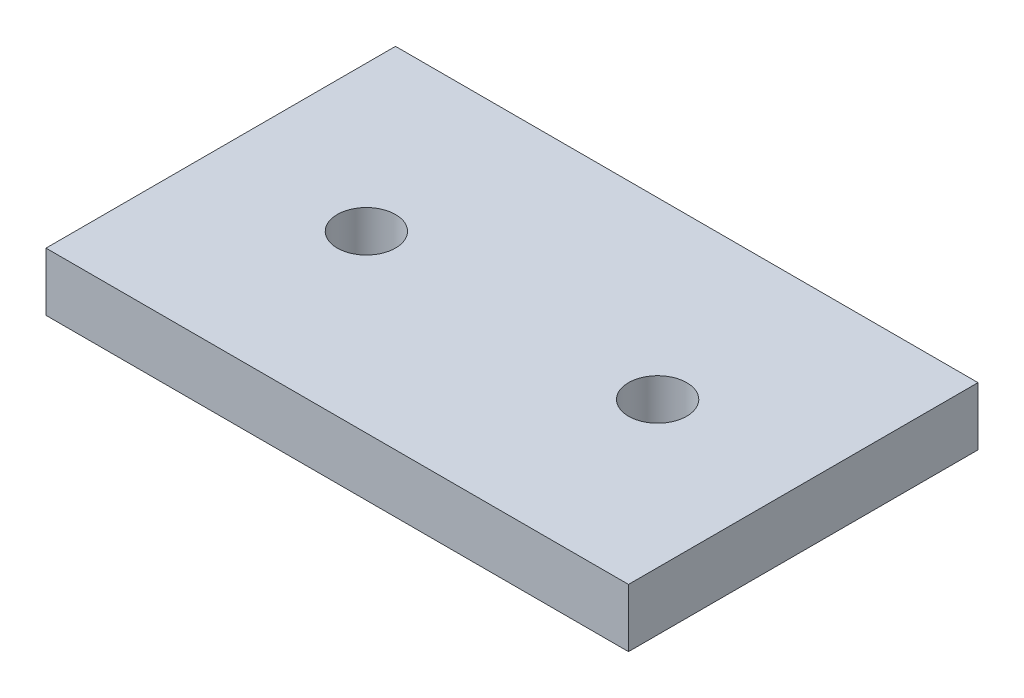
SolidWorks part; units mm, degrees
ref_plane "Спереди" through (0, 0, 0) normal (0, 0, 1) x (1, 0, 0)
ref_plane "Сверху" through (0, 0, 0) normal (0, 1, 0) x (1, 0, 0)
ref_plane "Справа" through (0, 0, 0) normal (1, 0, 0) x (0, 0, -1)
sketch "Эскиз1" plane through (0, 0, 0) normal (0, 1, 0) x (1, 0, 0)
  line L1 (0, 0) -> (100, 0)
  line L2 (0, 0) -> (0, 60)
  line L3 (0, 60) -> (100, 60)
  line L4 (100, 0) -> (100, 60)
extrude "Бобышка-Вытянуть1" add sketch "Эскиз1" along normal blind 10
sketch "Эскиз2" plane through (0, 10, 0) normal (0, 1, 0) x (1, 0, 0)
  circle A0 centre (25, 30) radius 5
  circle A1 centre (75, 30) radius 5
  dimension "D1" = 2
extrude "Вырез-Вытянуть1" cut sketch "Эскиз2" against normal through all
